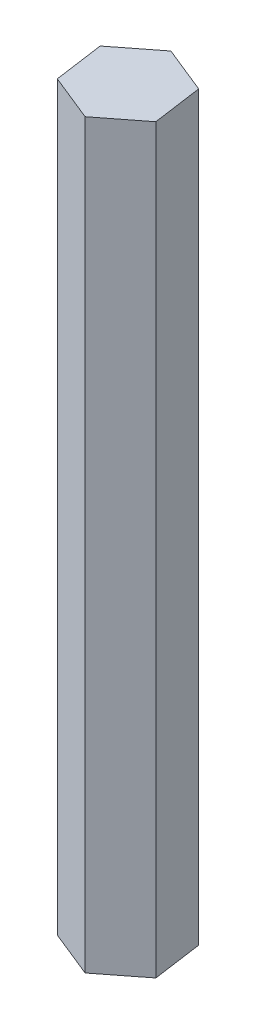
SolidWorks part; units mm, degrees
ref_plane "Front Plane" through (0, 0, 0) normal (0, 0, 1) x (1, 0, 0)
ref_plane "Top Plane" through (0, 0, 0) normal (0, 1, 0) x (1, 0, 0)
ref_plane "Right Plane" through (0, 0, 0) normal (1, 0, 0) x (0, 0, -1)
sketch "Sketch1" plane through (0, 0, 0) normal (0, 1, 0) x (1, 0, 0)
  line L1 (5.7787, 4.5133) -> (-1.0193, 7.2612)
  line L2 (-1.0193, 7.2612) -> (-6.798, 2.7479)
  line L3 (-6.798, 2.7479) -> (-5.7787, -4.5133)
  line L4 (-5.7787, -4.5133) -> (1.0193, -7.2612)
  line L5 (1.0193, -7.2612) -> (6.798, -2.7479)
  line L6 (6.798, -2.7479) -> (5.7787, 4.5133)
  circle A0 centre (0, 0) radius 6.35 construction
  point P1 (6.2883, 0.8827)
  dimension "D1" = 12.7
extrude "Boss-Extrude1" add sketch "Sketch1" along normal blind 107.95
equation "\"ˊ\"=0.1"
